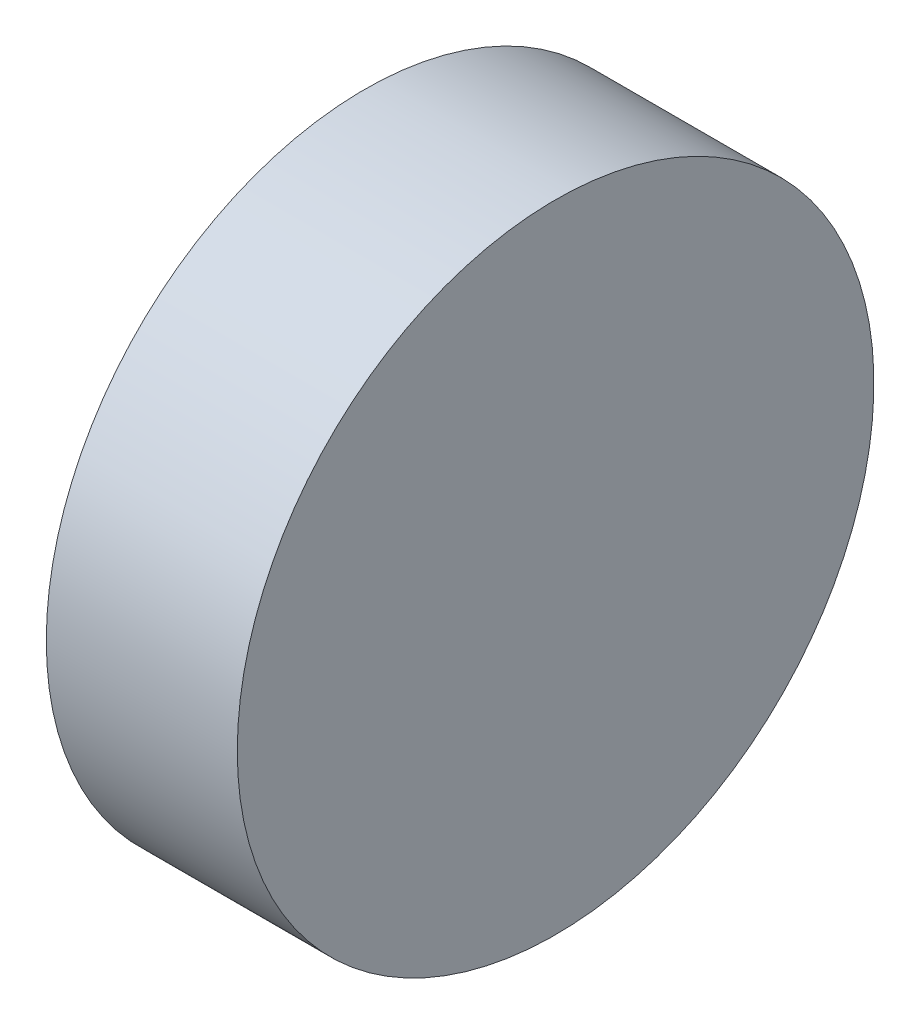
SolidWorks part; units mm, degrees
ref_plane "前视基准面" through (0, 0, 0) normal (0, 0, 1) x (1, 0, 0)
ref_plane "上视基准面" through (0, 0, 0) normal (0, 1, 0) x (1, 0, 0)
ref_plane "右视基准面" through (0, 0, 0) normal (1, 0, 0) x (0, 0, -1)
sketch "草图1" plane through (0, 0, 0) normal (0, 0, 1) x (1, 0, 0)
  line L0 (169.3339, 51.5288) -> (184.2078, 51.5288) construction
  line L1 (173.4187, 51.5288) -> (173.4187, 61.5288)
  line L2 (179.4187, 51.5288) -> (179.4187, 61.5288)
  line L3 (173.4187, 51.5288) -> (179.4187, 51.5288)
  line L5 (173.4187, 61.5288) -> (179.4187, 61.5288)
revolve "旋转1" add sketch "草图1" angle 360 about L0
